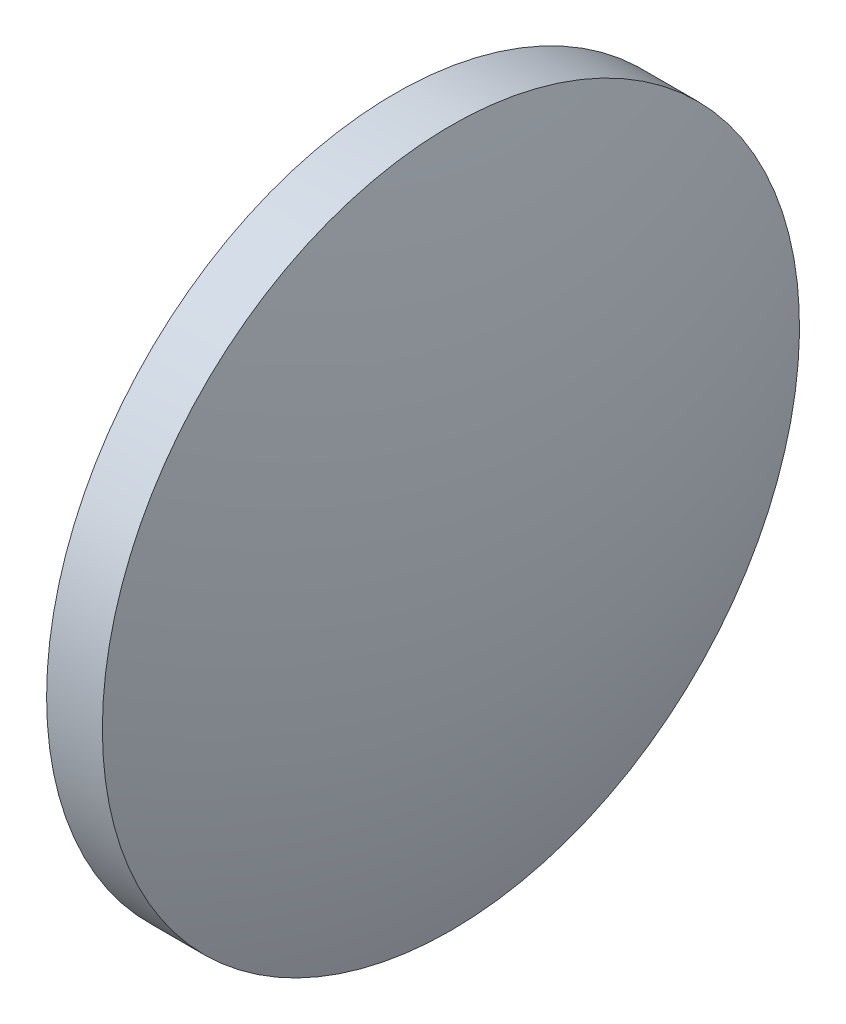
SolidWorks part; units mm, degrees
ref_plane "前视基准面" through (0, 0, 0) normal (0, 0, 1) x (1, 0, 0)
ref_plane "上视基准面" through (0, 0, 0) normal (0, 1, 0) x (1, 0, 0)
ref_plane "右视基准面" through (0, 0, 0) normal (1, 0, 0) x (0, 0, -1)
sketch "草图1" plane through (0, 0, 0) normal (0, 0, 1) x (1, 0, 0)
  line L0 (850.1959, 251.6067) -> (846.2559, 251.6067)
  line L7 (843.8903, 251.6067) -> (853.4784, 251.6067) construction
  line L8 (846.2559, 251.6067) -> (846.2559, 264.1067)
  line L12 (846.2559, 264.1067) -> (848.2559, 264.1067)
  arc A1 (850.1959, 251.6067) -> (848.2559, 264.1067) centre (808.9553, 251.6067) ccw
revolve "旋转2" add sketch "草图1" angle 360 about L7
